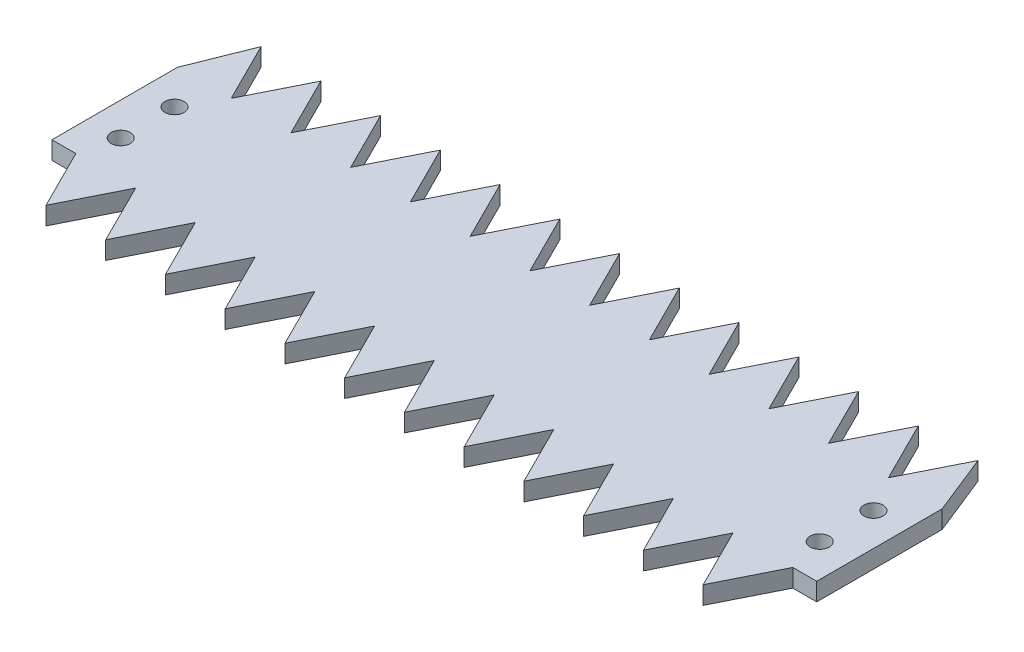
SolidWorks part; units mm, degrees
ref_plane "Front Plane" through (0, 0, 0) normal (0, 0, 1) x (1, 0, 0)
ref_plane "Top Plane" through (0, 0, 0) normal (0, 1, 0) x (1, 0, 0)
ref_plane "Right Plane" through (0, 0, 0) normal (1, 0, 0) x (0, 0, -1)
sketch "Sketch1" plane through (0, 0, 0) normal (0, 1, 0) x (1, 0, 0)
  line L1 (-64, -20.5) -> (64, -20.5)
  line L2 (-64, -20.5) -> (-64, 20.5)
  line L3 (-64, 20.5) -> (64, 20.5)
  line L4 (64, -20.5) -> (64, 20.5)
  line L5 (-64, -20.5) -> (64, 20.5) construction
  line L6 (-64, 20.5) -> (64, -20.5) construction
  point P0 (0, 0)
  dimension "D1" = 128
  dimension "D2" = 41
extrude "Boss-Extrude1" add sketch "Sketch1" along normal blind 3
sketch "Sketch2" plane through (0, 3, 0) normal (0, 1, 0) x (1, 0, 0)
  line L0 (-60, 20.5) -> (-55, 10.5)
  line L1 (-55, 10.5) -> (-50, 20.5)
  line L3 (64, 20.5) -> (-64, 20.5) construction
  line L4 (-50, 20.5) -> (-60, 20.5)
  line L5 (-64, 20.5) -> (-64, -20.5) construction
  dimension "D1" = 10
  dimension "D2" = 10
  dimension "D3" = 4
extrude "Cut-Extrude2" cut sketch "Sketch2" against normal through all both and the other way through all
pattern_linear "LPattern3" count 12 spacing 10 along (1, 0, 0) of "Cut-Extrude2"
sketch "Sketch5" plane through (0, 3, 0) normal (0, 1, 0) x (1, 0, 0)
  line L0 (-60, -10.5) -> (-55, -20.5)
  line L2 (-64, -20.5) -> (64, -20.5) construction
  line L3 (-55, -20.5) -> (-50, -10.5)
  line L4 (-50, -10.5) -> (-50, -20.5)
  line L5 (-50, -20.5) -> (-60, -20.5)
  line L6 (-60, -20.5) -> (-60, -10.5)
  line M27 (-64, -20.5) -> (64, -20.5)
  dimension "D1" = 10
  dimension "D2" = 10
  dimension "D3" = 4
extrude "Cut-Extrude3" cut sketch "Sketch5" against normal through all both and the other way through all contours L6 L0 M27 | L4 L3 M27
pattern_linear "LPattern5" count 12 spacing 10 along (1, 0, 0) of "Cut-Extrude3"
sketch "Sketch6" plane through (0, 3, 0) normal (0, 1, 0) x (1, 0, 0)
  circle A0 centre (-58.5, 4.5) radius 1.6
  dimension "D1" = 3.2
  dimension "D2" = 58.5
  dimension "D3" = 4.5
extrude "Cut-Extrude4" cut sketch "Sketch6" against normal through all both and the other way through all
mirror "Mirror2" about plane through (0, 0, 0) normal (1, 0, 0) of "Cut-Extrude4"
mirror "Mirror3" about plane through (0, 0, 0) normal (0, 0, 1) of "Mirror2", "Cut-Extrude4"
sketch "Sketch7" plane through (0, 3, 0) normal (0, 1, 0) x (1, 0, 0)
  line L0 (-60, 20.5) -> (-64, 10.5)
  line L1 (-64, 20.5) -> (-64, -20.5) construction
  line L2 (-64, 10.5) -> (-64, 20.5)
  line L3 (-64, 20.5) -> (-60, 20.5)
  dimension "D1" = 10
extrude "Cut-Extrude5" cut sketch "Sketch7" against normal through all both and the other way through all
mirror "Mirror4" about plane through (0, 0, 0) normal (1, 0, 0) of "Cut-Extrude5"
sketch "Sketch8" plane through (0, 3, 0) normal (0, 1, 0) x (1, 0, 0)
  line L1 (-60, -10.5) -> (-64, -10.5)
  line L2 (-60, -10.5) -> (-60, -20.5)
  line L3 (-60, -20.5) -> (-64, -20.5)
  line L4 (-64, -10.5) -> (-64, -20.5)
extrude "Cut-Extrude6" cut sketch "Sketch8" against normal through all both and the other way through all
mirror "Mirror5" about plane through (0, 0, 0) normal (1, 0, 0) of "Cut-Extrude6"
